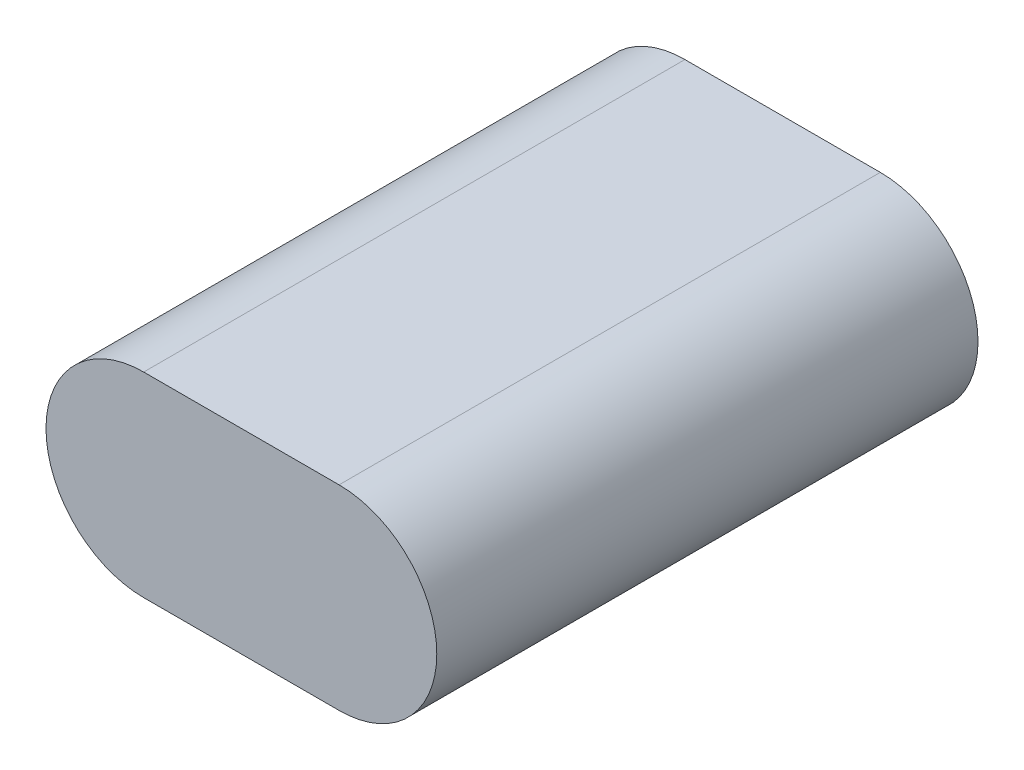
SolidWorks part; units mm, degrees
ref_plane "前视基准面" through (0, 0, 0) normal (0, 0, 1) x (1, 0, 0)
ref_plane "上视基准面" through (0, 0, 0) normal (0, 1, 0) x (1, 0, 0)
ref_plane "右视基准面" through (0, 0, 0) normal (1, 0, 0) x (0, 0, -1)
other "质心 (COM)"
sketch "草图1" plane through (0, 0, 0) normal (0, 0, 1) x (1, 0, 0)
  line L0 (-50, 50) -> (50, 50)
  line L4 (-50, -50) -> (50, -50)
  arc A2 (-50, 50) -> (-50, -50) centre (-50, 0) ccw
  arc A3 (50, 50) -> (50, -50) centre (50, 0) cw
  point P8 (0, -50)
  point P10 (0, 50)
extrude "凸台-拉伸1" add sketch "草图1" along normal mid plane 277
